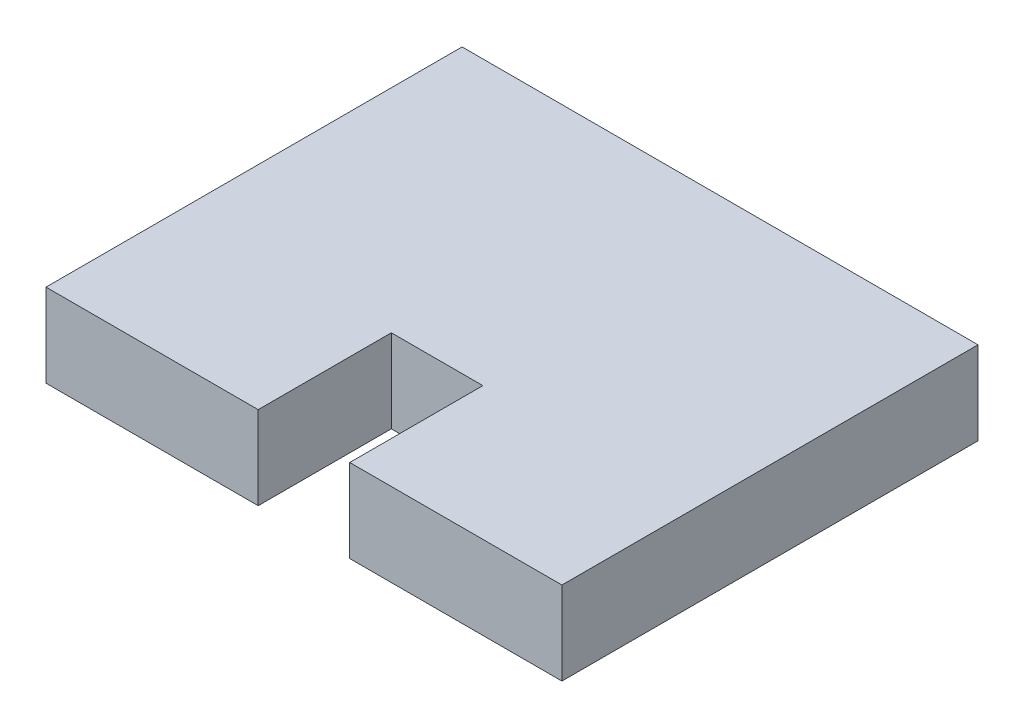
SolidWorks part; units mm, degrees
ref_plane "Alzado" through (0, 0, 0) normal (0, 0, 1) x (1, 0, 0)
ref_plane "Planta" through (0, 0, 0) normal (0, 1, 0) x (1, 0, 0)
ref_plane "Vista lateral" through (0, 0, 0) normal (1, 0, 0) x (0, 0, -1)
sketch "Croquis1" plane through (0, 0, 0) normal (0, 1, 0) x (1, 0, 0)
  line L1 (-15.5, -12.5) -> (15.5, -12.5)
  line L2 (-15.5, -12.5) -> (-15.5, 12.5)
  line L3 (-15.5, 12.5) -> (15.5, 12.5)
  line L4 (15.5, -12.5) -> (15.5, 12.5)
  line L5 (-15.5, -12.5) -> (15.5, 12.5) construction
  line L6 (-15.5, 12.5) -> (15.5, -12.5) construction
  point P0 (0, 0)
  dimension "D1" = 25
  dimension "D2" = 31
extrude "Saliente-Extruir1" add sketch "Croquis1" along normal blind 5
sketch "Croquis2" plane through (0, 5, 0) normal (0, 1, 0) x (1, 0, 0)
  line L0 (0, 12.5) -> (0, -12.5) construction
  line L1 (15.5, 12.5) -> (-15.5, 12.5) construction
  line L2 (-15.5, -12.5) -> (15.5, -12.5) construction
  line L4 (-2.75, -12.5) -> (2.75, -12.5)
  line L5 (-2.75, -12.5) -> (-2.75, -4.5)
  line L6 (-2.75, -4.5) -> (2.75, -4.5)
  line L7 (2.75, -12.5) -> (2.75, -4.5)
  line L8 (-2.75, -12.5) -> (2.75, -4.5) construction
  line L9 (-2.75, -4.5) -> (2.75, -12.5) construction
  point P6 (0, -8.5)
  dimension "D1" = 5.5
  dimension "D2" = 8
  dimension "D3" = 0
extrude "Cortar-Extruir1" cut sketch "Croquis2" against normal blind 5
